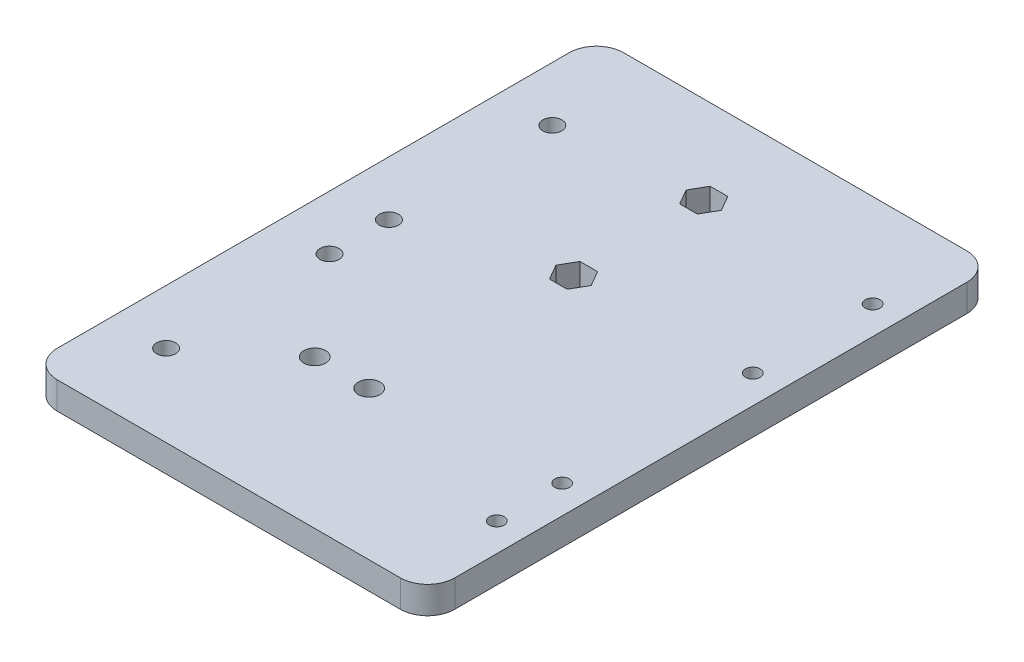
SolidWorks part; units mm, degrees
ref_plane "Front Plane" through (0, 0, 0) normal (0, 0, 1) x (1, 0, 0)
ref_plane "Top Plane" through (0, 0, 0) normal (0, 1, 0) x (1, 0, 0)
ref_plane "Right Plane" through (0, 0, 0) normal (1, 0, 0) x (0, 0, -1)
sketch "Sketch1" plane through (-157.389, 183.7846, -475.4244) normal (0, 1, 0) x (1, 0, 0)
  line L1 (0, 0) -> (75, 0)
  line L2 (0, 0) -> (0, 104)
  line L3 (0, 104) -> (75, 104)
  line L4 (75, 0) -> (75, 104)
  dimension "D1" = 75
  dimension "D2" = 104
extrude "Boss-Extrude1" add sketch "Sketch1" along normal blind 5
sketch "Sketch2" plane through (0, 188.7846, 0) normal (0, 1, 0) x (1, 0, 0)
  line L0 (-82.389, 579.4244) -> (-157.389, 579.4244) construction
  line L1 (-157.389, 475.4244) -> (-82.389, 475.4244) construction
  line L2 (-157.389, 579.4244) -> (-157.389, 475.4244) construction
  circle A0 centre (-145.389, 490.4244) radius 1.75
  circle A1 centre (-145.389, 520.4244) radius 1.75
  circle A2 centre (-145.389, 531.3244) radius 1.75
  circle A3 centre (-145.389, 561.3244) radius 1.75
  dimension "D1" = 3.5
  dimension "D2" = 30
  dimension "D3" = 30
  dimension "D4" = 18.1
  dimension "D5" = 15
  dimension "D6" = 12
extrude "Cut-Extrude1" cut sketch "Sketch2" against normal through all
sketch "Sketch3" plane through (0, 183.7846, 0) normal (0, -1, 0) x (1, 0, 0)
  line L0 (-116.3559, -563.3306) -> (-117.9724, -566.1306)
  line L1 (-117.9724, -566.1306) -> (-121.2056, -566.1306)
  line L2 (-121.2056, -566.1306) -> (-122.8222, -563.3306)
  line L3 (-122.8222, -563.3306) -> (-121.2056, -560.5306)
  line L4 (-121.2056, -560.5306) -> (-117.9724, -560.5306)
  line L5 (-117.9724, -560.5306) -> (-116.3559, -563.3306)
  line L6 (-82.389, -579.4244) -> (-157.389, -579.4244) construction
  line L7 (-157.389, -579.4244) -> (-157.389, -475.4244) construction
  line L8 (-116.3527, -539.4232) -> (-117.9693, -542.2232)
  line L9 (-117.9693, -542.2232) -> (-121.2024, -542.2232)
  line L10 (-121.2024, -542.2232) -> (-122.819, -539.4232)
  line L11 (-122.819, -539.4232) -> (-121.2024, -536.6232)
  line L12 (-121.2024, -536.6232) -> (-117.9693, -536.6232)
  line L13 (-117.9693, -536.6232) -> (-116.3527, -539.4232)
  line L14 (-157.389, -475.4244) -> (-82.389, -475.4244) construction
  circle A0 centre (-87.589, -493.3306) radius 1.35
  circle A1 centre (-87.589, -505.3306) radius 1.35
  circle A2 centre (-87.589, -540.3306) radius 1.35
  circle A3 centre (-87.589, -562.3306) radius 1.35
  circle A6 centre (-130.389, -502.7008) radius 2
  circle A7 centre (-120.389, -502.7008) radius 2
  dimension "D11" = 2.7
  dimension "D12" = 2.7
  dimension "D13" = 12
  dimension "D14" = 17.9062
  dimension "D15" = 69.8
  dimension "D16" = 69.8
  dimension "D17" = 2.7
  dimension "D18" = 2.7
  dimension "D19" = 22
  dimension "D20" = 39.0938
  dimension "D21" = 69.8
  dimension "D22" = 69.8
  dimension "D23" = 4
  dimension "D24" = 4
  dimension "D1" = 3.2332
  dimension "D2" = 16.0938
  dimension "D3" = 34.5668
  dimension "D4" = 120
  dimension "D5" = 120
  dimension "D6" = 120
  dimension "D7" = 120
  dimension "D8" = 40.0012
  dimension "D9" = 34.57
  dimension "D10" = 3.2332
extrude "Cut-Extrude2" cut sketch "Sketch3" against normal through all
sketch "Sketch4" plane through (0, 183.7846, 0) normal (0, -1, 0) x (1, 0, 0)
  line L0 (-82.389, -579.4244) -> (-157.389, -579.4244) construction
  line L1 (-157.389, -475.4244) -> (-155.389, -475.4244)
  line L2 (-157.389, -475.4244) -> (-157.389, -579.4244)
  line L3 (-157.389, -579.4244) -> (-155.389, -579.4244)
  line L4 (-155.389, -475.4244) -> (-155.389, -579.4244)
  dimension "D1" = 2
extrude "Cut-Extrude3" cut sketch "Sketch4" against normal through all
fillet "Fillet1" radius 5 4 edges at (-82.389, 186.2846, -579.4244) (-155.389, 186.2846, -579.4244) (-155.389, 186.2846, -475.4244) (-82.389, 186.2846, -475.4244)
